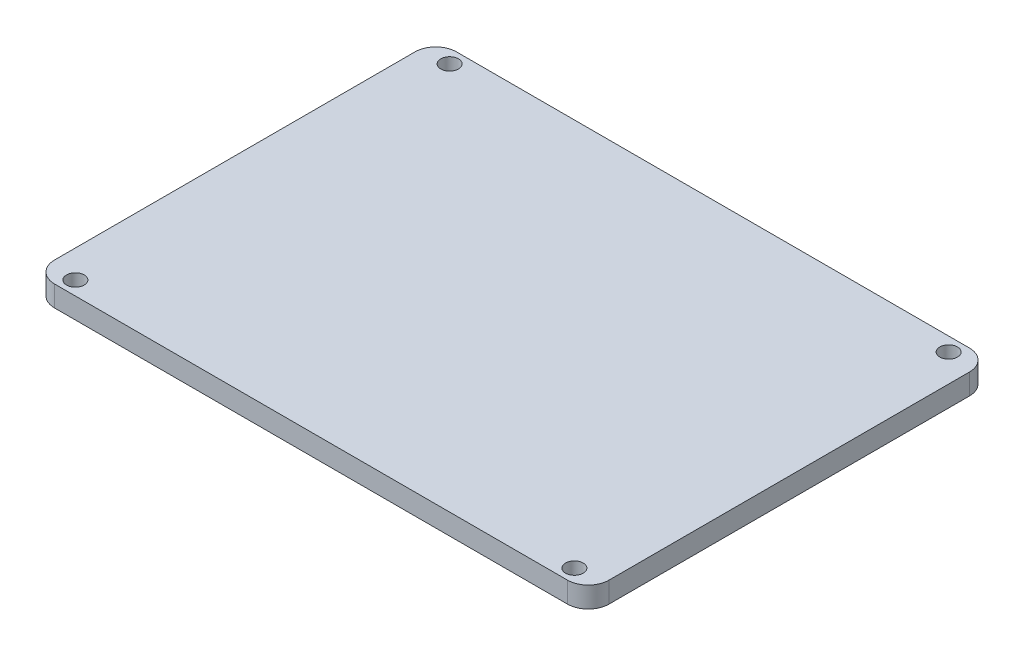
SolidWorks part; units mm, degrees
material "Thornel Mat VMA"
ref_plane "前视基准面" through (0, 0, 0) normal (0, 0, 1) x (1, 0, 0)
ref_plane "上视基准面" through (0, 0, 0) normal (0, 1, 0) x (1, 0, 0)
ref_plane "右视基准面" through (0, 0, 0) normal (1, 0, 0) x (0, 0, -1)
other "Configuration Table"
sketch "草图1" plane through (0, 0, 0) normal (0, 1, 0) x (1, 0, 0)
  line L1 (-40, -29) -> (40, -29)
  line L2 (-40, -29) -> (-40, 29)
  line L3 (-40, 29) -> (40, 29)
  line L4 (40, -29) -> (40, 29)
  line L5 (-40, -29) -> (40, 29) construction
  line L6 (-40, 29) -> (40, -29) construction
  point P0 (0, 0)
  dimension "D1" = 80
  dimension "D2" = 58
extrude "凸台-拉伸1" add sketch "草图1" along normal blind 3
sketch "草图2" plane through (0, 3, 0) normal (0, 1, 0) x (1, 0, 0)
  line L1 (36, -27) -> (-36, -27) construction
  line L2 (36, -27) -> (36, 27) construction
  line L3 (36, 27) -> (-36, 27) construction
  line L4 (-36, -27) -> (-36, 27) construction
  line L5 (36, -27) -> (-36, 27) construction
  line L6 (36, 27) -> (-36, -27) construction
  circle A0 centre (36, -27) radius 1.275
  circle A1 centre (36, 27) radius 1.275
  circle A2 centre (-36, 27) radius 1.275
  circle A3 centre (-36, -27) radius 1.275
  point P0 (0, 0)
  dimension "D1" = 2.55
  dimension "D2" = 54
  dimension "D3" = 72
extrude "切除-拉伸1" cut sketch "草图2" against normal through all both and the other way through all
fillet "圆角1" radius 3 4 edges at (40, 1.5, 29) (-40, 1.5, 29) (40, 1.5, -29) (-40, 1.5, -29)
